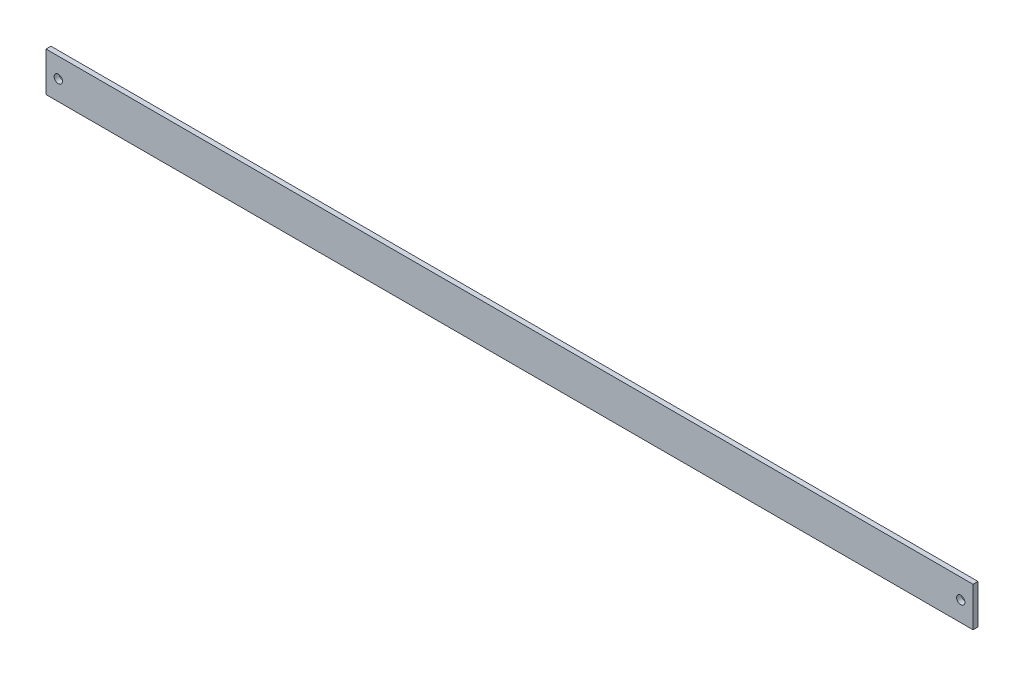
SolidWorks part; units mm, degrees
ref_plane "Front" through (0, 0, 0) normal (0, 0, 1) x (1, 0, 0)
ref_plane "Top" through (0, 0, 0) normal (0, 1, 0) x (1, 0, 0)
ref_plane "Right" through (0, 0, 0) normal (1, 0, 0) x (0, 0, -1)
sketch "Sketch1" plane through (0, 0, 0) normal (1, 0, 0) x (0, 0, -1)
  line L1 (0, 0) -> (3.175, 0)
  line L2 (0, 0) -> (0, 25.4)
  line L3 (0, 25.4) -> (3.175, 25.4)
  line L4 (3.175, 0) -> (3.175, 25.4)
  line L5 (0, 0) -> (3.175, 25.4) construction
  line L6 (0, 25.4) -> (3.175, 0) construction
  point P4 (1.5875, 12.7)
  dimension "D1" = 25.4
  dimension "D2" = 3.175
extrude "Boss-Extrude1" add sketch "Sketch1" along normal blind 596.9
sketch "Sketch2" plane through (0, 0, 0) normal (0, 0, 1) x (1, 0, 0)
  line L0 (7.9375, 12.7) -> (0, 12.7) construction
  line L1 (0, 25.4) -> (0, 0) construction
  line L2 (588.9625, 12.7) -> (596.9, 12.7) construction
  line L3 (596.9, 25.4) -> (596.9, 0) construction
  circle A0 centre (7.9375, 12.7) radius 2.667
  circle A1 centre (588.9625, 12.7) radius 2.667
  dimension "D1" = 5.334
  dimension "D2" = 5.334
  dimension "D3" = 581.025
extrude "Cut-Extrude1" cut sketch "Sketch2" against normal up to next
